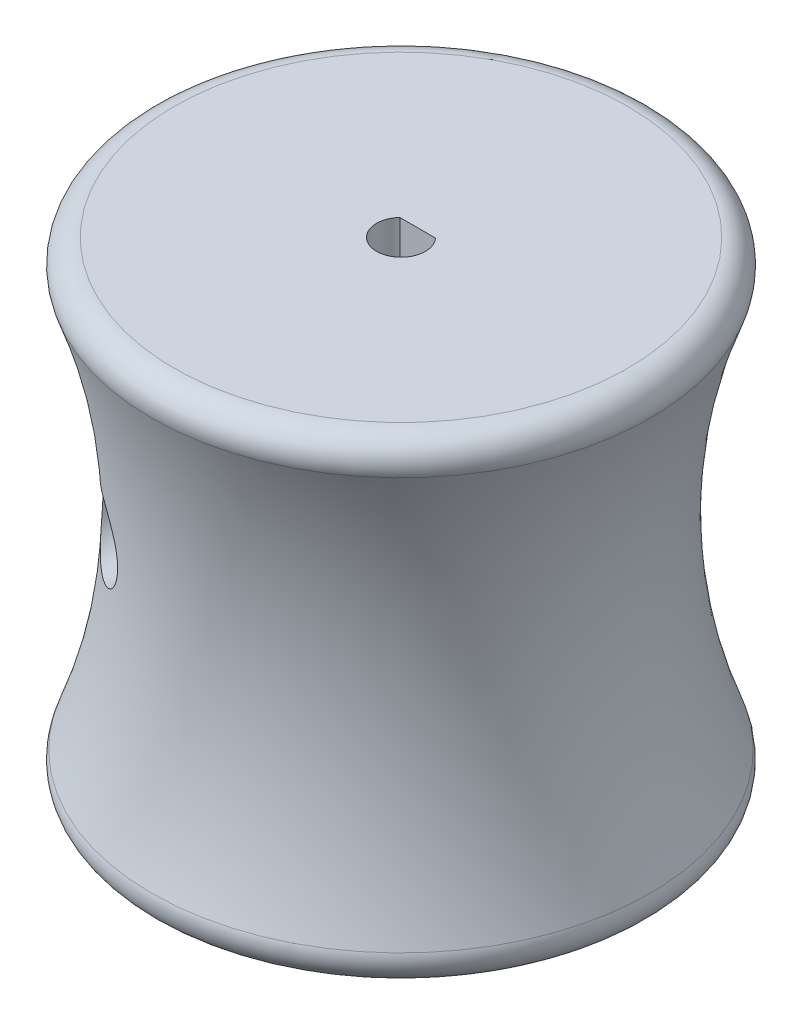
SolidWorks part; units mm, degrees
ref_plane "Plan de face" through (0, 0, 0) normal (0, 0, 1) x (1, 0, 0)
ref_plane "Plan de dessus" through (0, 0, 0) normal (0, 1, 0) x (1, 0, 0)
ref_plane "Plan de droite" through (0, 0, 0) normal (1, 0, 0) x (0, 0, -1)
sketch "Esquisse1" plane through (0, 0, 0) normal (0, 0, 1) x (1, 0, 0)
  line L0 (0, 0) -> (0, 16.5231) construction
  line L1 (-2.05, 0) -> (-2.05, 40)
  line L2 (-2.05, 40) -> (-22.05, 40)
  line L3 (-2.05, 0) -> (-22.05, 0)
  arc A2 (-22.05, 40) -> (-22.05, 0) centre (-67.2, 20) cw
  point P8 (-89.086, 20)
  dimension "D1" = 2.05
  dimension "D2" = 20
  dimension "D3" = 0
  dimension "D5" = 40
revolve "Révolution1" add sketch "Esquisse1" angle 360 about L0
fillet "Congé1" radius 2 2 edges at (0, 40, -22.05) (0, 0, -22.05)
sketch "Esquisse2" plane through (0, 40, 0) normal (0, 1, 0) x (1, 0, 0)
  line L0 (-1.5, 1.3973) -> (1.5, 1.3973)
  circle A0 centre (0, 0) radius 2.05 construction
  arc A1 (1.5, 1.3973) -> (-1.5, 1.3973) centre (0, 0) ccw
  dimension "D1" = 3
extrude "Boss.-Extru.1" add sketch "Esquisse2" against normal up to surface (40 mm away) up to face at (0, 0, 19.0747)
sketch "Esquisse3" plane through (0, 0, 0) normal (0, 0, 1) x (1, 0, 0)
  line L0 (0, 0) -> (0, 40) construction
  line L1 (2.05, 40) -> (-2.05, 40) construction
  line L2 (0, 20) -> (-10.8218, 20) construction
  circle A0 centre (-10.8218, 20) radius 3
  dimension "D1" = 6
extrude "Enlèv. mat.-Extru.1" cut sketch "Esquisse3" against normal through all both and the other way through all
